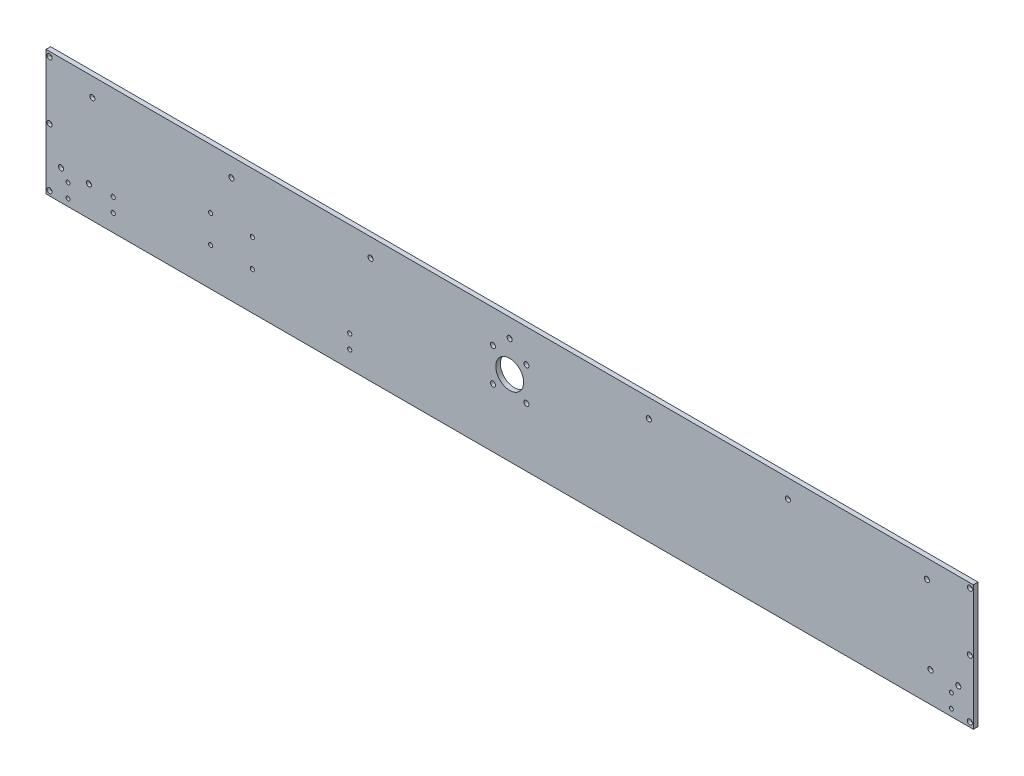
SolidWorks part; units mm, degrees
material "A3钢"
ref_plane "前视基准面" through (0, 0, 0) normal (0, 0, 1) x (1, 0, 0)
ref_plane "上视基准面" through (0, 0, 0) normal (0, 1, 0) x (1, 0, 0)
ref_plane "右视基准面" through (0, 0, 0) normal (1, 0, 0) x (0, 0, -1)
sketch "草图1" plane through (0, 0, 0) normal (0, 0, 1) x (1, 0, 0)
  line L1 (-1000, -135) -> (1000, -135)
  line L2 (-1000, -135) -> (-1000, 135)
  line L3 (-1000, 135) -> (1000, 135)
  line L4 (1000, -135) -> (1000, 135)
  line L5 (-1000, -135) -> (1000, 135) construction
  line L6 (-1000, 135) -> (1000, -135) construction
  point P0 (0, 0)
  dimension "D1" = 2000
  dimension "D2" = 270
extrude "凸台-拉伸1" add sketch "草图1" along normal mid plane 10
sketch "草图2" plane through (0, 0, 5) normal (0, 0, 1) x (1, 0, 0)
  line L0 (0, 619.8775) -> (0, -680.849) construction
  line L1 (-1000, 135) -> (-1000, -135) construction
  line L2 (-992.5, -125) -> (992.5, -125)
  line L3 (-992.5, -125) -> (-992.5, 125)
  line L4 (-992.5, 125) -> (992.5, 125)
  line L5 (992.5, -125) -> (992.5, 125)
  line L6 (-992.5, -125) -> (992.5, 125) construction
  line L7 (-992.5, 125) -> (992.5, -125) construction
  line L8 (-992.5, 0) -> (1266.3795, 0) construction
  point P3 (0, 0)
  dimension "D1" = 7.5
  dimension "D2" = 250
hole_wizard "打孔尺寸(%根据)内六角圆柱头螺钉的类型1" positions "3D草图1" profile "草图3" counterbore size "M6" standard "GB" end condition through all
sketch3d "3D草图1"
  line L0 (992.5, -125, 5) -> (992.5, 125, 5) construction
  point P0 (-992.5, 125, 5)
  point P3 (-992.5, -125, 5)
  point P6 (992.5, 125, 5)
  point P9 (992.5, -125, 5)
  point P12 (992.5, 0, 5)
  point P14 (-992.5, 0, 5)
sketch "草图3" plane through (-992.5, 125, 5) normal (1, 0, 0) x (0, -1, 0)
  line L0 (0, 0) -> (0, 10)
  line L1 (0, 10) -> (3.3, 10)
  line L3 (3.3, 10) -> (3.3, 6.8)
  line L4 (3.3, 6.8) -> (5.5, 6.8)
  line L5 (5.5, 6.8) -> (5.5, 0)
  line L7 (5.5, 0) -> (0, 0)
  line L11 (0, -6.35) -> (0, 107.95) construction
  dimension "通孔孔直径" = 6.6
  dimension "通孔孔深度" = 10
  dimension "柱形沉头孔直径" = 11
  dimension "柱形沉头孔深度" = 6.8
sketch "草图4" plane through (0, 0, 5) normal (0, 0, 1) x (1, 0, 0)
  line L0 (-660, -70) -> (-330, -70) construction
  line L1 (-330, -70) -> (330, -70) construction
  line L2 (330, -70) -> (660, -70) construction
  line L4 (-1000, -135) -> (1000, -135) construction
  line L5 (0, -500.4396) -> (0, 557.8999) construction
  dimension "D1" = 65
  dimension "D2" = 660
  dimension "D3" = 330
sketch "草图7" plane through (0, 0, 5) normal (0, 0, 1) x (1, 0, 0)
  line L0 (1000, -135) -> (1000, 135) construction
  line L1 (-1000, -135) -> (1000, -135) construction
  line L2 (952.5, -120) -> (952.5, -90) construction
  circle A0 centre (952.5, -120) radius 4
  dimension "D1" = 47.5
  dimension "D2" = 15
  dimension "D3" = 8
  dimension "D4" = 30
hole_wizard "M10 螺纹孔1" positions "3D草图4" profile "草图9" tap size "M10" standard "GB" end condition through all
sketch3d "3D草图4"
  point P4 (952.5, -120, 5)
  point P9 (952.5, -90, 5)
sketch "草图9" plane through (952.5, -120, 5) normal (1, 0, 0) x (0, -1, 0)
  line L0 (0, 0) -> (0, 10)
  line L1 (0, 10) -> (4.25, 10)
  line L2 (4.25, 10) -> (4.25, 0)
  line L5 (4.25, 0) -> (0, 0)
  line L11 (0, -6.35) -> (0, 107.95) construction
  dimension "通孔螺纹孔钻头直径" = 8.5
  dimension "通孔螺纹孔钻头深度" = 10
cosmetic thread "孔螺蚊线1" parameters "D2"=10
cosmetic thread "孔螺蚊线2" parameters "D2"=10
sketch "草图10" plane through (0, 0, 5) normal (0, 0, 1) x (1, 0, 0)
  line L0 (-1000, -70) -> (-967.5, -70) construction
  line L1 (-967.5, -70) -> (-907.5, -70) construction
  line L3 (-1000, 135) -> (-1000, -135) construction
  line L4 (-1000, -135) -> (1000, -135) construction
  dimension "D1" = 60
  dimension "D2" = 32.5
  dimension "D3" = 65
sketch "草图13" plane through (0, 0, -5) normal (0, 0, -1) x (-1, 0, 0)
  line L0 (600, 239.8087) -> (600, -409.6798) construction
  line L1 (1000, -135) -> (-1000, -135) construction
  line L2 (345, -98) -> (855, -98)
  line L3 (345, -98) -> (345, -68)
  line L4 (345, -68) -> (855, -68)
  line L5 (855, -98) -> (855, -68)
  line L6 (345, -98) -> (855, -68) construction
  line L7 (345, -68) -> (855, -98) construction
  point P3 (600, -83)
  dimension "D1" = 510
  dimension "D2" = 30
  dimension "D3" = 37
  dimension "D4" = 600
hole_wizard "Ø9.0 (9) 直径孔3" positions "3D草图6" profile "草图14" hole size "Ø9.0" standard "GB" end condition through all
sketch3d "3D草图6"
  point P0 (-345, -68, -5)
  point P3 (-345, -98, -5)
  point P6 (-855, -68, -5)
  point P9 (-855, -98, -5)
sketch "草图14" plane through (-345, -68, -5) normal (1, 0, 0) x (0, 1, 0)
  line L0 (0, 0) -> (0, 10)
  line L1 (0, 10) -> (4.5, 10)
  line L2 (4.5, 10) -> (4.5, 0)
  line L5 (4.5, 0) -> (0, 0)
  line L11 (0, -6.35) -> (0, 107.95) construction
  dimension "通孔孔直径" = 9
  dimension "通孔孔深度" = 10
sketch "草图15" plane through (0, 0, -5) normal (0, 0, -1) x (-1, 0, 0)
  line L0 (0, 162) -> (0, -87.2009) construction
  line L1 (0, 0) -> (0, 219.6539) construction
  line L3 (-36, 64) -> (36, 64)
  line L4 (1000, -135) -> (-1000, -135) construction
  line L5 (-50, -2) -> (50, -2)
  line L6 (-50, -2) -> (-50, 58)
  line L7 (-50, 58) -> (50, 58)
  line L8 (50, -2) -> (50, 58)
  line L9 (-50, -2) -> (50, 58) construction
  line L10 (-50, 58) -> (50, -2) construction
  line L11 (-36, 64) -> (-36, -8)
  line L12 (-36, -8) -> (36, -8)
  line L13 (36, 64) -> (36, -8)
  line L14 (-36, 64) -> (36, -8) construction
  line L15 (-36, -8) -> (36, 64) construction
  point P6 (0, 28)
  point P11 (0, 28)
  dimension "D1" = 100
  dimension "D2" = 60
  dimension "D3" = 133
  dimension "D5" = 72
sketch "草图17" plane through (0, 0, -5) normal (0, 0, -1) x (-1, 0, 0)
  line L0 (0, 0) -> (0, 418.4231) construction
  line L2 (555, -53) -> (645, -53)
  line L3 (555, -53) -> (555, 7)
  line L4 (555, 7) -> (645, 7)
  line L5 (645, -53) -> (645, 7)
  line L6 (555, -53) -> (645, 7) construction
  line L7 (555, 7) -> (645, -53) construction
  line L8 (1000, -135) -> (-1000, -135) construction
  point P3 (600, -23)
  dimension "D1" = 112
  dimension "D2" = 90
  dimension "D3" = 60
  dimension "D4" = 600
hole_wizard "Ø9.0 (9) 直径孔4" positions "3D草图8" profile "草图18" hole size "Ø9.0" standard "GB" end condition through all
sketch3d "3D草图8"
  point P0 (-555, 7, -5)
  point P3 (-645, 7, -5)
  point P6 (-645, -53, -5)
  point P9 (-555, -53, -5)
sketch "草图18" plane through (-555, 7, -5) normal (1, 0, 0) x (0, 1, 0)
  line L0 (0, 0) -> (0, 10)
  line L1 (0, 10) -> (4.5, 10)
  line L2 (4.5, 10) -> (4.5, 0)
  line L5 (4.5, 0) -> (0, 0)
  line L11 (0, -6.35) -> (0, 107.95) construction
  dimension "通孔孔直径" = 9
  dimension "通孔孔深度" = 10
hole_wizard "Ø11.0 (11) 直径孔1" positions "3D草图9" profile "草图19" hole size "Ø11.0" standard "GB" end condition through all
sketch3d "3D草图9"
  point P0 (36, -8, -5)
  point P3 (-36, -8, -5)
  point P6 (-36, 64, -5)
  point P9 (36, 64, -5)
sketch "草图19" plane through (36, -8, -5) normal (1, 0, 0) x (0, 1, 0)
  line L0 (0, 0) -> (0, 10)
  line L1 (0, 10) -> (5.5, 10)
  line L2 (5.5, 10) -> (5.5, 0)
  line L5 (5.5, 0) -> (0, 0)
  line L11 (0, -6.35) -> (0, 107.95) construction
  dimension "通孔孔直径" = 11
  dimension "通孔孔深度" = 10
sketch "草图20" plane through (0, 0, -5) normal (0, 0, -1) x (-1, 0, 0)
  circle A0 centre (0, 28) radius 30
  dimension "D1" = 60
extrude "切除-拉伸1" cut sketch "草图20" against normal through all
sketch "草图21" plane through (0, 0, 5) normal (0, 0, 1) x (1, 0, 0)
  line L0 (0, 135) -> (0, -135) construction
  line L1 (1000, 135) -> (-1000, 135) construction
  line L2 (-1000, -135) -> (1000, -135) construction
  line L3 (0, 95) -> (-300, 95) construction
  line L4 (-300, 95) -> (-600, 95) construction
  line L5 (-600, 95) -> (-900, 95) construction
  line L6 (300, 95) -> (600, 95) construction
  line L7 (600, 95) -> (900, 95) construction
  dimension "D1" = 40
  dimension "D2" = 300
hole_wizard "打孔尺寸(%根据)内六角圆柱头螺钉的类型5" positions "3D草图10" profile "草图22" counterbore size "M6" standard "GB" end condition through all
sketch3d "3D草图10"
  point P0 (-900, 95, 5)
  point P3 (-600, 95, 5)
  point P6 (-300, 95, 5)
  point P9 (0, 95, 5)
  point P12 (300, 95, 5)
  point P15 (600, 95, 5)
  point P18 (900, 95, 5)
sketch "草图22" plane through (-900, 95, 5) normal (1, 0, 0) x (0, -1, 0)
  line L0 (0, 0) -> (0, 10)
  line L1 (0, 10) -> (3.3, 10)
  line L3 (3.3, 10) -> (3.3, 6.8)
  line L4 (3.3, 6.8) -> (5.5, 6.8)
  line L5 (5.5, 6.8) -> (5.5, 0)
  line L7 (5.5, 0) -> (0, 0)
  line L11 (0, -6.35) -> (0, 107.95) construction
  dimension "通孔孔直径" = 6.6
  dimension "通孔孔深度" = 10
  dimension "柱形沉头孔直径" = 11
  dimension "柱形沉头孔深度" = 6.8
mirror "镜向1" about plane through (0, 0, 0) normal (1, 0, 0) of "M10 螺纹孔1"
sketch "草图23" plane through (0, 0, 5) normal (0, 0, 1) x (1, 0, 0)
  line L0 (907.5, -70) -> (967.5, -70) construction
  line L1 (1000, -135) -> (1000, 135) construction
  line L2 (-1000, -135) -> (1000, -135) construction
  dimension "D1" = 60
  dimension "D2" = 32.5
  dimension "D3" = 65
hole_wizard "打孔尺寸(%根据)内六角圆柱头螺钉的类型6" positions "3D草图11" profile "草图24" counterbore size "M6" standard "GB" end condition through all
sketch3d "3D草图11"
  point P0 (907.5, -70, 5)
  point P3 (967.5, -70, 5)
sketch "草图24" plane through (907.5, -70, 5) normal (1, 0, 0) x (0, -1, 0)
  line L0 (0, 0) -> (0, 10)
  line L1 (0, 10) -> (3.3, 10)
  line L3 (3.3, 10) -> (3.3, 6.8)
  line L4 (3.3, 6.8) -> (5.5, 6.8)
  line L5 (5.5, 6.8) -> (5.5, 0)
  line L7 (5.5, 0) -> (0, 0)
  line L11 (0, -6.35) -> (0, 107.95) construction
  dimension "通孔孔直径" = 6.6
  dimension "通孔孔深度" = 10
  dimension "柱形沉头孔直径" = 11
  dimension "柱形沉头孔深度" = 6.8
mirror "镜向2" about plane through (0, 0, 0) normal (1, 0, 0) of "打孔尺寸(%根据)内六角圆柱头螺钉的类型6"
